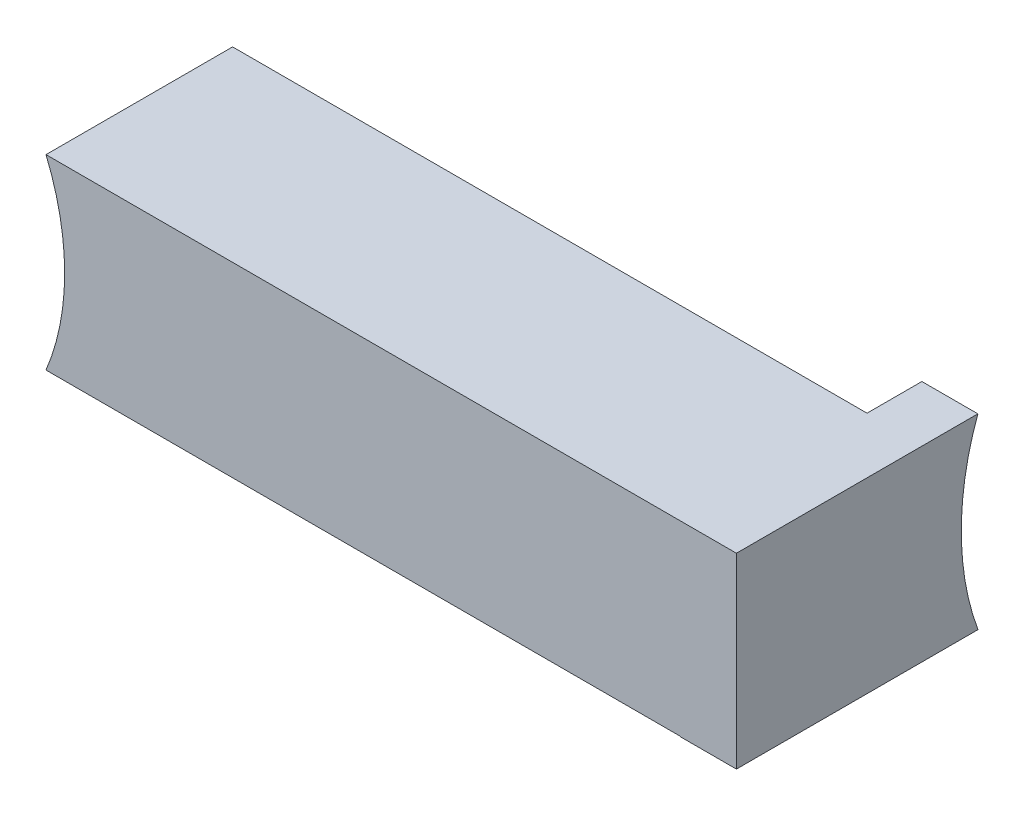
SolidWorks part; units mm, degrees
ref_plane "Plano frontal" through (0, 0, 0) normal (0, 0, 1) x (1, 0, 0)
ref_plane "Plano superior" through (0, 0, 0) normal (0, 1, 0) x (1, 0, 0)
ref_plane "Plano direito" through (0, 0, 0) normal (1, 0, 0) x (0, 0, -1)
sketch "Esboço1" plane through (0, 0, 0) normal (1, 0, 0) x (0, 0, -1)
  line L0 (-5, 0) -> (0, 0) construction
  line L1 (-5, 5) -> (5, 5)
  line L2 (-5, 5) -> (-5, -5)
  line L3 (-5, -5) -> (5, -5)
  line L4 (5, 5) -> (5, -5)
  line L5 (0, 0) -> (0, -5) construction
  dimension "D1" = 10
  dimension "D2" = 10
extrude "Extrusão1" add sketch "Esboço1" against normal blind 40
sketch "Esboço2" plane through (0, 0, 0) normal (1, 0, 0) x (0, 0, -1)
  line L1 (-5, 5) -> (9.2296, 5)
  line L2 (-5, 5) -> (-5, -5.0202)
  line L3 (-5, -5.0202) -> (9.2296, -5.0202)
  line L4 (9.2296, 5) -> (9.2296, -5.0202)
extrude "Extrusão2" add sketch "Esboço2" against normal blind 3
sketch "Esboço3" plane through (0, 0, 0) normal (1, 0, 0) x (0, 0, -1)
  line L0 (5, 5) -> (5, -5) construction
  circle A0 centre (21.55, 0) radius 14.5
  dimension "D1" = 29
  dimension "D2" = 16.55
extrude "Corte-extrusão1" cut sketch "Esboço3" against normal blind 23
sketch "Esboço4" plane through (0, 0, 5) normal (0, 0, 1) x (1, 0, 0)
  line L0 (0, 5) -> (0, -5.0202) construction
  circle A0 centre (-49, 0) radius 13
  dimension "D1" = 26
  dimension "D2" = 49
extrude "Corte-extrusão2" cut sketch "Esboço4" against normal blind 23
